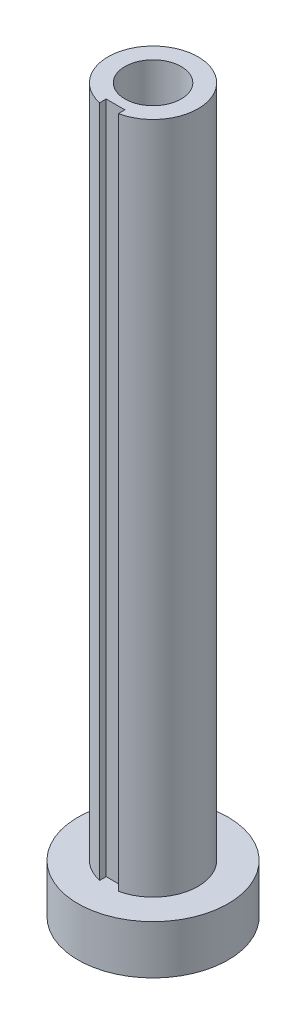
SolidWorks part; units mm, degrees
ref_plane "Front" through (0, 0, 0) normal (0, 0, 1) x (1, 0, 0)
ref_plane "Top" through (0, 0, 0) normal (0, 1, 0) x (1, 0, 0)
ref_plane "Right" through (0, 0, 0) normal (1, 0, 0) x (0, 0, -1)
sketch "Sketch1" plane through (0, 0, 0) normal (0, 1, 0) x (1, 0, 0)
  circle A0 centre (0, 0) radius 6.096
  circle A1 centre (0, 0) radius 3.81
  dimension "D1" = 12.192
  dimension "D2" = 7.62
extrude "Boss-Extrude1" add sketch "Sketch1" along normal blind 97.79
sketch "Sketch2" plane through (0, 0, 0) normal (0, -1, 0) x (1, 0, 0)
  line L0 (0, 5.08) -> (0, 0) construction
  line L1 (-1.27, 6.7077) -> (1.27, 6.7077)
  line L2 (-1.27, 6.7077) -> (-1.27, 5.08)
  line L3 (-1.27, 5.08) -> (1.27, 5.08)
  line L4 (1.27, 6.7077) -> (1.27, 5.08)
  dimension "D2" = 5.08
  dimension "D3" = 2.54
extrude "Cut-Extrude1" cut sketch "Sketch2" against normal through all both and the other way through all
sketch "Sketch3" plane through (0, 0, 0) normal (0, -1, 0) x (1, 0, 0)
  circle A0 centre (0, 0) radius 10.16
  circle A1 centre (0, 0) radius 3.81 construction
  circle A2 centre (0, 0) radius 3.81
  dimension "D1" = 20.32
extrude "Boss-Extrude2" add sketch "Sketch3" against normal blind 6.604
